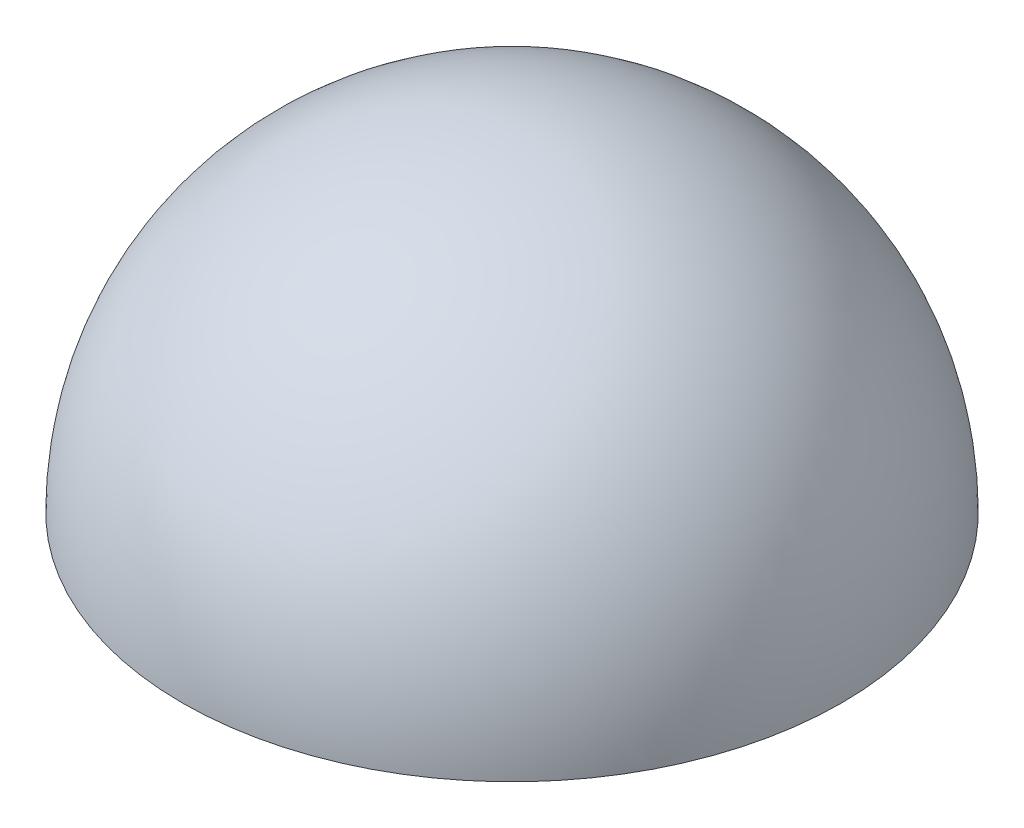
SolidWorks part; units mm, degrees
ref_plane "Front Plane" through (0, 0, 0) normal (0, 0, 1) x (1, 0, 0)
ref_plane "Top Plane" through (0, 0, 0) normal (0, 1, 0) x (1, 0, 0)
ref_plane "Right Plane" through (0, 0, 0) normal (1, 0, 0) x (0, 0, -1)
sketch "Sketch1" plane through (0, 0, 0) normal (0, 0, 1) x (1, 0, 0)
  line L0 (-12.7, 0) -> (-13.2, 0)
  line L2 (0, 0) -> (0, 15.033) construction
  line L3 (0, 13.2) -> (0, 12.7)
  arc A0 (-12.7, 0) -> (0, 12.7) centre (0, 0) cw
  arc A1 (-13.2, 0) -> (0, 13.2) centre (0, 0) cw
  dimension "D1" = 12.7
  dimension "D2" = 13.2
revolve "Revolve2" add sketch "Sketch1" angle 360 about L2
equation "\"dia_difflayer\"= 13"
equation "\"dia_outer_out\"= 12.5"
equation "\"dia_outer_in\"= 12"
equation "\"dia_inner_out\"= 11"
equation "\"dia_inner_in\"= 10.5"
equation "\"degrees\"= 12.5"
equation "\"d_marker\"= 1"
equation "\"t_marker\"= 0.5"
equation "\"n_markers_1\"= 6"
equation "\"n_markers_2\"= round ( 6 * sin ( 2*\"degrees\" ) / sin ( \"degrees\" ) )"
equation "\"n_markers_3\"= round ( 6 * sin ( 3*\"degrees\" ) / sin ( \"degrees\" ) )"
equation "\"n_markers_4\"= round ( 6 * sin ( 4*\"degrees\" ) / sin ( \"degrees\" ) )"
equation "\"n_markers_5\"= round ( 6 * sin ( 5*\"degrees\" ) / sin ( \"degrees\" ) )"
equation "\"n_teeth\"= 8"
